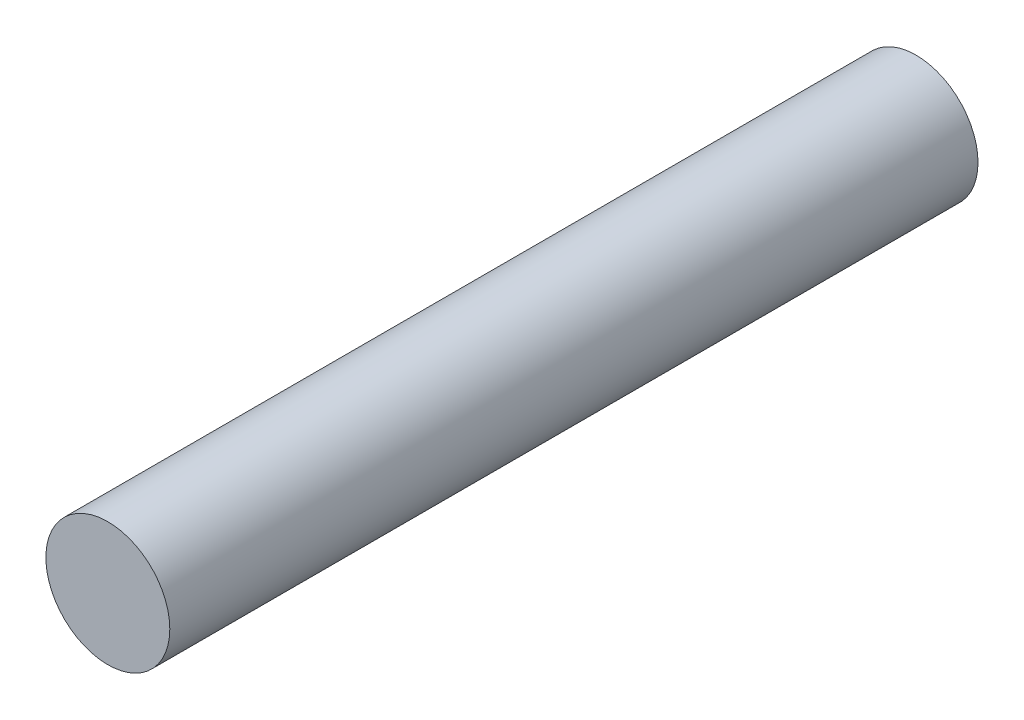
SolidWorks part; units mm, degrees
material "AISI 304"
ref_plane "Front Plane" through (0, 0, 0) normal (0, 0, 1) x (1, 0, 0)
ref_plane "Top Plane" through (0, 0, 0) normal (0, 1, 0) x (1, 0, 0)
ref_plane "Right Plane" through (0, 0, 0) normal (1, 0, 0) x (0, 0, -1)
sketch "Sketch1" plane through (0, 0, 0) normal (0, 0, 1) x (1, 0, 0)
  circle A0 centre (0, 0) radius 1.4605
  dimension "D1" = 2.921
extrude "Boss-Extrude1" add sketch "Sketch1" along normal blind 19.05
